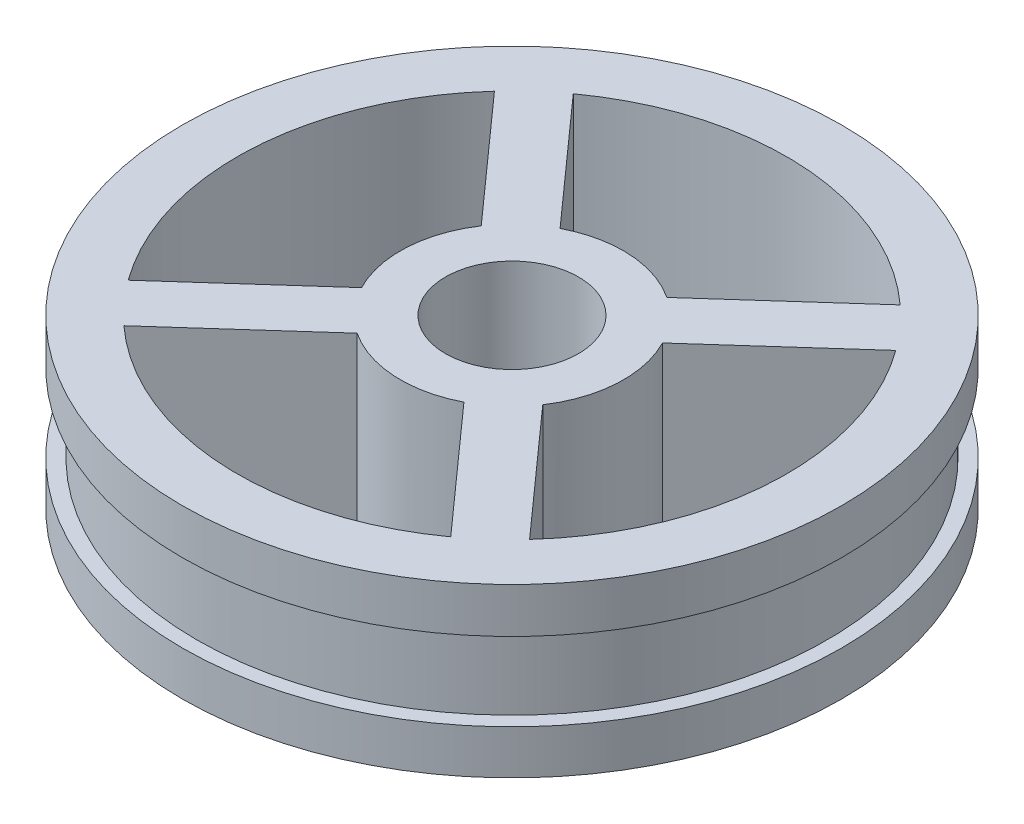
SolidWorks part; units mm, degrees
ref_plane "Front Plane" through (0, 0, 0) normal (0, 0, 1) x (1, 0, 0)
ref_plane "Top Plane" through (0, 0, 0) normal (0, 1, 0) x (1, 0, 0)
ref_plane "Right Plane" through (0, 0, 0) normal (1, 0, 0) x (0, 0, -1)
sketch "Sketch1" plane through (0, 0, 0) normal (0, 1, 0) x (1, 0, 0)
  circle A0 centre (0, 0) radius 30
  circle A1 centre (0, 0) radius 25
extrude "Boss-Extrude1" add sketch "Sketch1" along normal blind 15.24 contours A1 | A0
sketch "Sketch2" plane through (0, 15.24, 0) normal (0, 1, 0) x (1, 0, 0)
  line L0 (31.8381, 31.9027) -> (35.2259, 28.1173)
  line L1 (-31.8381, -31.9027) -> (35.2259, 28.1173)
  line L2 (-35.2259, -28.1173) -> (31.8381, 31.9027)
  line L3 (31.8649, -31.876) -> (28.0755, -35.2593)
  line L4 (31.8649, -31.876) -> (-28.0755, 35.2593)
  line L5 (28.0755, -35.2593) -> (-31.8649, 31.876)
  line L6 (-35.2259, -28.1173) -> (-31.8381, -31.9027)
  spline S0 degree 1 poles (-31.8649, 31.876) (-28.0755, 35.2593) knots 0 0 1 1
  circle M7 centre (0, 0) radius 25
extrude "Boss-Extrude2" add sketch "Sketch2" against normal up to surface (15.24 mm away) contours L5 L1 L4 L2 | L4 L1 L2 M7 | L5 L2 L4 M7 | L1 L5 L2 M7 | L5 L4 L1 M7 up to face at (0, 0, 30)
sketch "Sketch3" plane through (0, 0, 0) normal (0, -1, 0) x (-1, 0, 0)
  circle A0 centre (0, 0) radius 10.16
  dimension "D1" = 20.32
extrude "Boss-Extrude3" add sketch "Sketch3" along normal blind 10 and the other way blind 15.24
sketch "Sketch5" plane through (0, -10, 0) normal (0, -1, 0) x (-1, 0, 0)
  circle A0 centre (0, 0) radius 5
sketch3d "3DSketch2" plane through (0, 0, 0) normal (0, 0, 1) x (1, 0, 0)
  dimension "D1" = 4.9911
sketch "Sketch14" plane through (0, 10.2489, 0) normal (0, 1, 0) x (1, 0, 0)
  circle A0 centre (0, 0) radius 38.1
  circle A1 centre (0, 0) radius 28.702
  dimension "D1" = 76.2
extrude "Cut-Extrude1" cut sketch "Sketch14" against normal blind 6.2263 and the other way blind 0.8923
sketch "Sketch17" plane through (0, 10.2489, 0) normal (0, 1, 0) x (1, 0, 0)
  circle A0 centre (0, 0) radius 38.1
  circle A1 centre (0, 0) radius 28.702
sketch "Sketch18" plane through (0, -10, 0) normal (0, -1, 0) x (1, 0, 0)
  line L1 (7.1857, 0) -> (3.5929, 6.223)
  line L2 (3.5929, 6.223) -> (-3.5929, 6.223)
  line L3 (-3.5929, 6.223) -> (-7.1857, 0)
  line L4 (-7.1857, 0) -> (-3.5929, -6.223)
  line L5 (-3.5929, -6.223) -> (3.5929, -6.223)
  line L6 (3.5929, -6.223) -> (7.1857, 0)
  circle A0 centre (0, 0) radius 6.223 construction
  dimension "D1" = 12.446
extrude "Cut-Extrude2" cut sketch "Sketch18" against normal blind 6.35
sketch "Sketch19" plane through (0, -3.65, 0) normal (0, -1, 0) x (1, 0, 0)
  circle A0 centre (0, 0) radius 2.032
extrude "Cut-Extrude3" cut sketch "Sketch19" against normal up to surface (18.89 mm away) up to face at (15.7957, 15.24, 0.8849)
sketch "Sketch20" plane through (0, 15.24, 0) normal (0, 1, 0) x (1, 0, 0)
  circle A0 centre (0, 0) radius 6.0521
extrude "Cut-Extrude4" cut sketch "Sketch20" against normal blind 15.24
